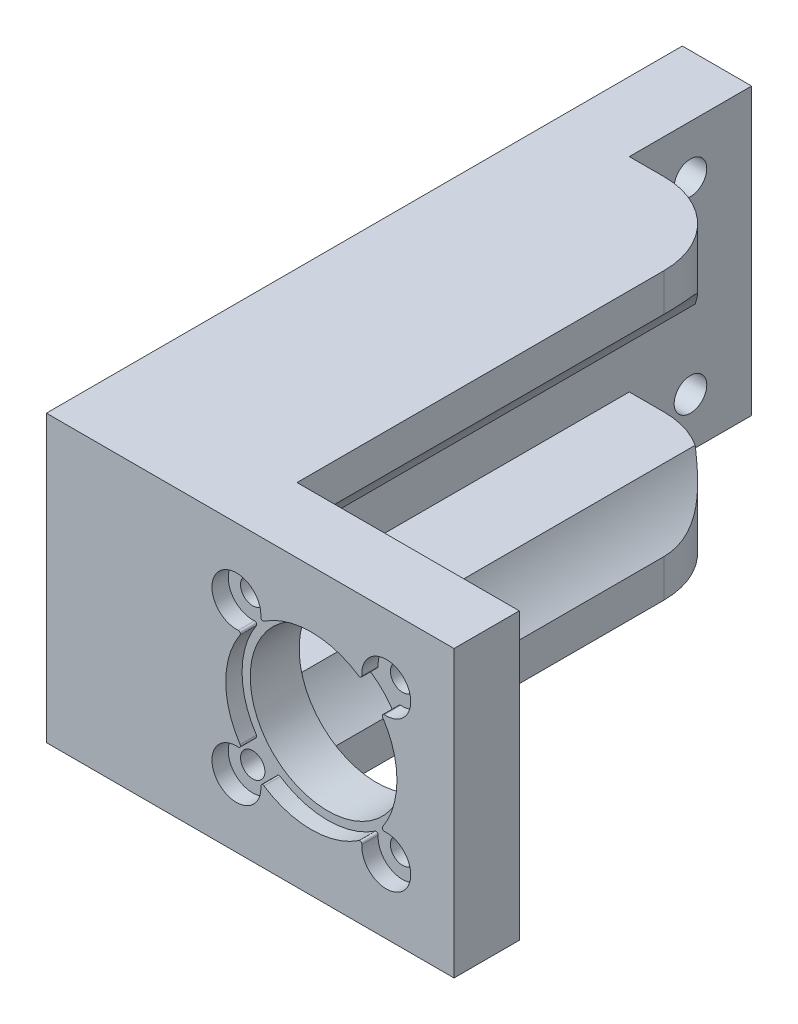
SolidWorks part; units mm, degrees
ref_plane "Piano frontale" through (0, 0, 0) normal (0, 0, 1) x (1, 0, 0)
ref_plane "Piano superiore" through (0, 0, 0) normal (0, 1, 0) x (1, 0, 0)
ref_plane "Piano destro" through (0, 0, 0) normal (1, 0, 0) x (0, 0, -1)
sketch "Sketch1" plane through (0, 0, 0) normal (0, 0, 1) x (1, 0, 0)
  line L0 (0, 17.5) -> (50, 17.5) construction
  line L1 (0, 0) -> (50, 0)
  line L2 (0, 0) -> (0, 35)
  line L3 (0, 35) -> (50, 35)
  line L4 (50, 0) -> (50, 35)
  line L5 (25, 35) -> (25, 0) construction
  line L6 (32.5, 17.5) -> (41.6924, 26.6924) construction
  line L7 (32.5, 17.5) -> (41.6924, 8.3076) construction
  line L8 (32.5, 17.5) -> (32.5, 0) construction
  line L9 (32.5, 17.5) -> (23.3076, 8.3076) construction
  line L10 (32.5, 17.5) -> (23.3076, 26.6924) construction
  circle A0 centre (32.5, 17.5) radius 9.5
  circle A1 centre (32.5, 17.5) radius 13 construction
  circle A2 centre (41.6924, 26.6924) radius 1.5
  circle A3 centre (41.6924, 8.3076) radius 1.5
  circle A4 centre (23.3076, 8.3076) radius 1.5
  circle A5 centre (23.3076, 26.6924) radius 1.5
  circle A6 centre (32.5, 17.5) radius 16 construction
  dimension "D2" = 19
  dimension "D4" = 26
  dimension "D6" = 3
  dimension "D7" = 17.5
  dimension "D9" = 32
  dimension "D1" = 50
  dimension "D3" = 17.5
  dimension "D5" = 45
  dimension "D8" = 35
extrude "Boss-Extrude3" add sketch "Sketch1" along normal blind 6
sketch "Sketch4" plane through (0, 0, 6) normal (0, 0, 1) x (1, 0, 0)
  line L0 (32.5, 17.5) -> (32.5, 34.7569) construction
  line L1 (32.5, 17.5) -> (32.5, 0) construction
  line L2 (0, 0) -> (50, 0) construction
  line L3 (32.5, 17.5) -> (0, 17.5) construction
  line L4 (0, 35) -> (0, 0) construction
  line L6 (0, 35) -> (50, 35)
  line L7 (0, 35) -> (0, 0)
  line L8 (0, 0) -> (50, 0)
  line L9 (50, 35) -> (50, 0)
  arc A0 (26.2994, 26.4708) -> (23.5292, 23.7006) centre (23.3076, 26.6924) ccw
  arc A1 (26.2994, 8.5292) -> (23.5292, 11.2994) centre (23.3076, 8.3076) cw
  arc A2 (38.7006, 8.5292) -> (41.4708, 11.2994) centre (41.6924, 8.3076) ccw
  arc A3 (38.7006, 26.4708) -> (41.4708, 23.7006) centre (41.6924, 26.6924) cw
  arc A4 (23.7558, 23.3129) -> (23.7558, 11.6871) centre (32.5, 17.5) ccw
  arc A5 (38.3129, 26.2442) -> (26.6871, 26.2442) centre (32.5, 17.5) ccw
  arc A6 (41.2442, 11.6871) -> (41.2442, 23.3129) centre (32.5, 17.5) ccw
  arc A7 (26.6871, 8.7558) -> (38.3129, 8.7558) centre (32.5, 17.5) ccw
  arc A8 (23.7558, 11.6871) -> (23.5292, 11.2994) centre (23.5476, 11.5487) cw
  arc A9 (26.6871, 8.7558) -> (26.2994, 8.5292) centre (26.5487, 8.5476) ccw
  arc A10 (38.3129, 8.7558) -> (38.7006, 8.5292) centre (38.4513, 8.5476) cw
  arc A11 (41.2442, 11.6871) -> (41.4708, 11.2994) centre (41.4524, 11.5487) ccw
  arc A12 (41.2442, 23.3129) -> (41.4708, 23.7006) centre (41.4524, 23.4513) cw
  arc A13 (38.3129, 26.2442) -> (38.7006, 26.4708) centre (38.4513, 26.4524) ccw
  arc A14 (26.6871, 26.2442) -> (26.2994, 26.4708) centre (26.5487, 26.4524) cw
  arc A15 (23.7558, 23.3129) -> (23.5292, 23.7006) centre (23.5476, 23.4513) ccw
  dimension "D1" = 6
  dimension "D2" = 21
  dimension "D3" = 0.25
extrude "Boss-Extrude5" add sketch "Sketch4" along normal blind 2
sketch "Sketch8" plane through (0, 0, 0) normal (0, 0, -1) x (-1, 0, 0)
  line L0 (-50, 35) -> (0, 35) construction
  line L1 (-22.7403, 35) -> (0, 35)
  line L2 (-22.7403, 35) -> (-22.7403, 30.3675)
  line L3 (-22.7403, 0) -> (0, 0)
  line L4 (0, 35) -> (0, 0)
  line L5 (-22.7403, 4.6325) -> (-22.7403, 0)
  line L6 (0, 35) -> (0, 0) construction
  line L7 (-16.35, 17.5) -> (-32.5, 17.5) construction
  line L8 (-8.5, 25) -> (-18.1947, 25)
  line L9 (0, 25) -> (0, 10)
  line L10 (-8.5, 10) -> (-18.1971, 10)
  line L11 (-18.1947, 25) -> (-18.1947, 24.9954)
  line L13 (0, 35) -> (-8.5, 35)
  line L14 (0, 35) -> (0, 0)
  line L15 (0, 0) -> (-8.5, 0)
  line L16 (-8.5, 25) -> (-8.5, 10)
  arc A0 (-22.7403, 4.6325) -> (-18.1971, 10) centre (-32.5, 17.5) ccw
  arc A1 (-18.1947, 24.9954) -> (-22.7403, 30.3675) centre (-32.5, 17.5) ccw
  line M3 (0, 0) -> (0, 35)
  line M4 (0, 35) -> (-50, 35)
  line M6 (-50, 0) -> (0, 0)
  dimension "D1" = 32.3
  dimension "D2" = 22.7403
  dimension "D3" = 15
  dimension "D4" = 18.1947
  dimension "D5" = 25
  dimension "D6" = 8.5
extrude "Boss-Extrude6" add sketch "Sketch8" along normal blind 55 contours A1 L11 L8 L16 L10 A0 L5 L3 L4 L1 L2 M6 M3 M4
sketch "Sketch9" plane through (0, 0, 0) normal (-1, 0, 0) x (0, 0, 1)
  line L0 (-55, 17.5) -> (8, 17.5) construction
  line L1 (-55, 0) -> (-55, 35) construction
  line L2 (8, 35) -> (8, 0) construction
  line L3 (-85, 17.5) -> (-22, 17.5) construction
  circle A0 centre (-7, 17.5) radius 2
  circle A1 centre (-37, 17.5) radius 2
  dimension "D1" = 4
  dimension "D2" = 15
  dimension "D3" = 2
extrude "Cut-Extrude1" cut sketch "Sketch9" against normal blind 8.5
sketch "Sketch11" plane through (0, 0, -55) normal (0, 0, -1) x (-1, 0, 0)
  line L1 (-18.1947, 24.9954) -> (-18.1947, 25)
  line L12 (-8.5, 10) -> (-8.5, 35)
  line L13 (0, 35) -> (-22.7403, 35) construction
  line L14 (-8.5, 10) -> (-8.5, 0)
  line L15 (-22.7403, 0) -> (0, 0) construction
  line L16 (-8.5, 0) -> (0, 0)
  line L17 (0, 0) -> (0, 35)
  line L18 (0, 35) -> (-8.5, 35)
  arc A0 (-18.1947, 24.9954) -> (-22.7403, 30.3675) centre (-32.5, 17.5) ccw construction
extrude "Boss-Extrude7" add sketch "Sketch11" along normal blind 15 contours L18 L12 L14 L16 L17
fillet "Fillet1" radius 10 3 edges at (20.1713, 27.932, -55) (18.1947, 24.9977, -55) (22.7403, 32.6837, -55)
fillet "Fillet8" radius 10 2 edges at (20.173, 7.066, -55) (22.7403, 2.3163, -55)
sketch "Sketch16" plane through (8.5, 0, 0) normal (1, 0, 0) x (0, 0, -1)
  line L0 (62.5, 35) -> (62.5, 0) construction
  line L1 (70, 35) -> (55, 35) construction
  line L2 (70, 0) -> (55, 0) construction
  line L3 (0, 17.5) -> (70, 17.5) construction
  line L4 (0, 25) -> (0, 10) construction
  line L5 (70, 0) -> (70, 35) construction
  circle A0 centre (62.5, 29) radius 2
  circle A1 centre (62.5, 6) radius 2
  dimension "D1" = 4
  dimension "D2" = 6
extrude "Cut-Extrude2" cut sketch "Sketch16" against normal blind 8.5
sketch "Sketch18" plane through (0, 0, 0) normal (-1, 0, 0) x (0, 0, 1)
  line L0 (-62.5, 29) -> (-62.5, 6) construction
  line L1 (-62.5, 17.5) -> (-37, 17.5) construction
  line L2 (-37, 17.5) -> (-7, 17.5) construction
